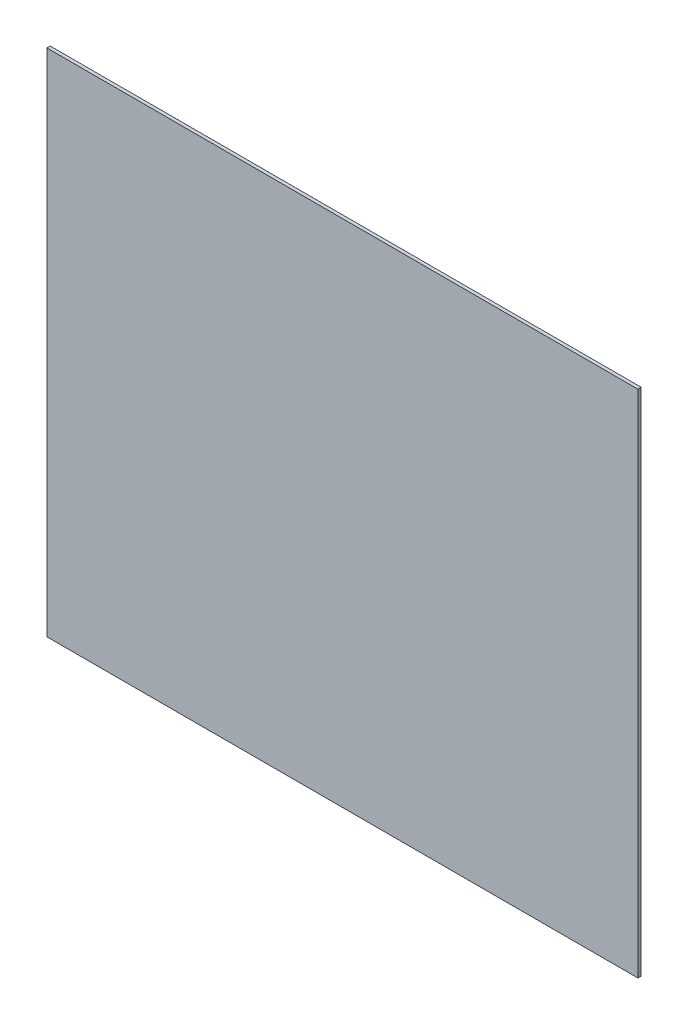
SolidWorks part; units mm, degrees
ref_plane "Plan de face" through (0, 0, 0) normal (0, 0, 1) x (1, 0, 0)
ref_plane "Plan de dessus" through (0, 0, 0) normal (0, 1, 0) x (1, 0, 0)
ref_plane "Plan de droite" through (0, 0, 0) normal (1, 0, 0) x (0, 0, -1)
sketch "Esquisse1" plane through (0, 0, 0) normal (0, 0, 1) x (1, 0, 0)
  line L1 (-67.1197, 30.2525) -> (472.8803, 30.2525)
  line L2 (-67.1197, 30.2525) -> (-67.1197, -435.7475)
  line L3 (-67.1197, -435.7475) -> (472.8803, -435.7475)
  line L4 (472.8803, 30.2525) -> (472.8803, -435.7475)
  dimension "D1" = 540
  dimension "D2" = 466
extrude "Boss.-Extru.1" add sketch "Esquisse1" along normal blind 3
equation "\"EpaisseurPlaque\"= 3"
equation "\"D1@Boss.-Extru.1\"=\"EpaisseurPlaque\""
equation "\"ProfondeurBoite\"=460"
equation "\"LongueurSyphon\"=270"
equation "\"LargeurSyphon\"=120"
equation "\"HauteurCoteDroit\"= 490"
equation "\"HauteurCoteGauche\"= 540"
equation "\"HauteurSolSyphon\"= 300"
equation "\"HauteurSyphon\"=\"HauteurCoteGauche\"-\"HauteurSolSyphon\""
equation "\"LargeurBoite\"= \"LargeurDroite\" + \"LargeurGauche\" + \"LargeurSyphon\""
equation "\"D2@Esquisse1\"=\"ProfondeurBoite\" + 2 *\"EpaisseurPlaque\""
equation "\"D1@Esquisse1\"=\"HauteurCoteGauche\" "
equation "\"LargeurDroite\"=10"
equation "\"LargeurGauche\"=150"
